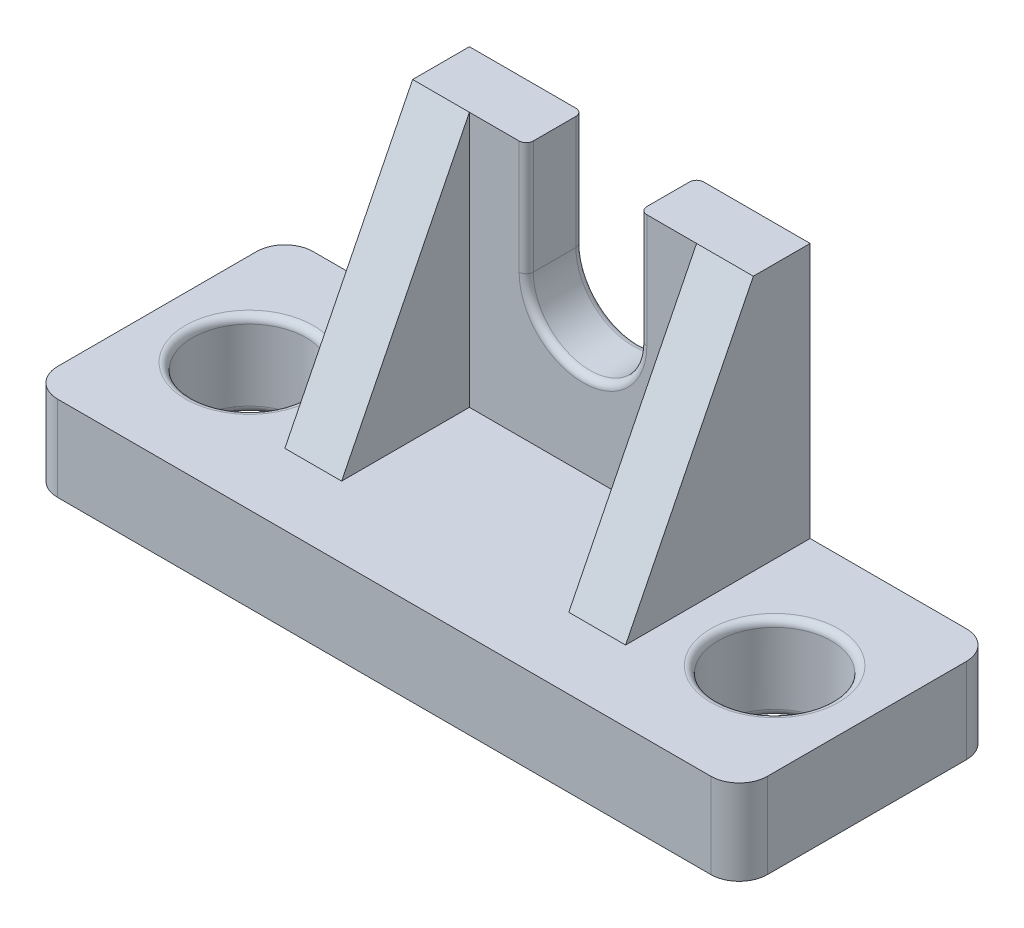
SolidWorks part; units mm, degrees
ref_plane "Front Plane" through (0, 0, 0) normal (0, 0, 1) x (1, 0, 0)
ref_plane "Top Plane" through (0, 0, 0) normal (0, 1, 0) x (1, 0, 0)
ref_plane "Right Plane" through (0, 0, 0) normal (1, 0, 0) x (0, 0, -1)
sketch "Sketch1" plane through (0, 0, 0) normal (0, 0, 1) x (1, 0, 0)
  line L1 (0, 0) -> (100, 0)
  line L2 (0, 0) -> (0, 12)
  line L3 (0, 12) -> (100, 12)
  line L4 (100, 0) -> (100, 12)
  dimension "D1" = 100
  dimension "D2" = 12
extrude "Boss-Extrude1" add sketch "Sketch1" against normal blind 36
sketch "Sketch2" plane through (0, 12, 0) normal (0, 1, 0) x (1, 0, 0)
  line L0 (50, 36) -> (50, 0) construction
  line L1 (100, 36) -> (0, 36) construction
  line L2 (100, 0) -> (0, 0) construction
  line L3 (0, 36) -> (0, 0) construction
  line L4 (26, 36) -> (74, 36)
  line L5 (26, 36) -> (26, 10)
  line L6 (26, 10) -> (74, 10)
  line L7 (74, 36) -> (74, 10)
  line L8 (100, 36) -> (100, 0) construction
  dimension "D1" = 26
  dimension "D2" = 26
  dimension "D3" = 10
extrude "Boss-Extrude2" add sketch "Sketch2" along normal blind 36
sketch "Sketch3" plane through (0, 48, 0) normal (0, 1, 0) x (1, 0, 0)
  line L1 (26, 10) -> (74, 10) construction
  line L2 (74, 36) -> (26, 36) construction
  line L3 (26, 36) -> (26, 10) construction
  line L4 (34, 10) -> (66, 10)
  line L5 (34, 10) -> (34, 28)
  line L6 (34, 28) -> (66, 28)
  line L7 (66, 10) -> (66, 28)
  line L8 (74, 10) -> (74, 36) construction
  dimension "D1" = 8
  dimension "D2" = 8
  dimension "D3" = 8
extrude "Cut-Extrude1" cut sketch "Sketch3" against normal blind 36
sketch "Sketch4" plane through (26, 0, 0) normal (-1, 0, 0) x (0, 0, 1)
  line L0 (-28, 48) -> (-10, 12)
  line L1 (-10, 12) -> (-10, 48)
  line L2 (-10, 48) -> (-10, 12) construction
  line L3 (-36, 48) -> (-10, 48) construction
  line L4 (-10, 48) -> (-28, 48)
  dimension "D1" = 8
extrude "Cut-Extrude2" cut sketch "Sketch4" against normal up to vertex
sketch "Sketch5" plane through (0, 0, -28) normal (0, 0, 1) x (1, 0, 0)
  line L0 (42, 48) -> (58, 48)
  line L1 (66, 48) -> (34, 48) construction
  line L2 (42, 32) -> (42, 48)
  line L3 (58, 32) -> (58, 48)
  arc A0 (42, 32) -> (58, 32) centre (50, 32) ccw
extrude "Cut-Extrude5" cut sketch "Sketch5" against normal blind 36
sketch "Sketch6" plane through (0, 12, 0) normal (0, 1, 0) x (1, 0, 0)
  circle A0 centre (13, 18) radius 8
  circle A1 centre (87, 18) radius 8
extrude "Cut-Extrude6" cut sketch "Sketch6" against normal blind 36
fillet "Fillet1" radius 4 4 edges at (100, 6, -36) (100, 6, 0) (0, 6, -36) (0, 6, 0)
fillet "Fillet2" radius 1 10 edges at (58, 40, -36) (42, 40, -36) (42, 40, -28) (58, 40, -28) (13, 0, -26) (87, 0, -26) (87, 12, -26) (13, 12, -10) (50, 24, -36) (50, 24, -28)
sketch "Sketch7" plane through (0, 48, 0) normal (0, 1, 0) x (1, 0, 0)
